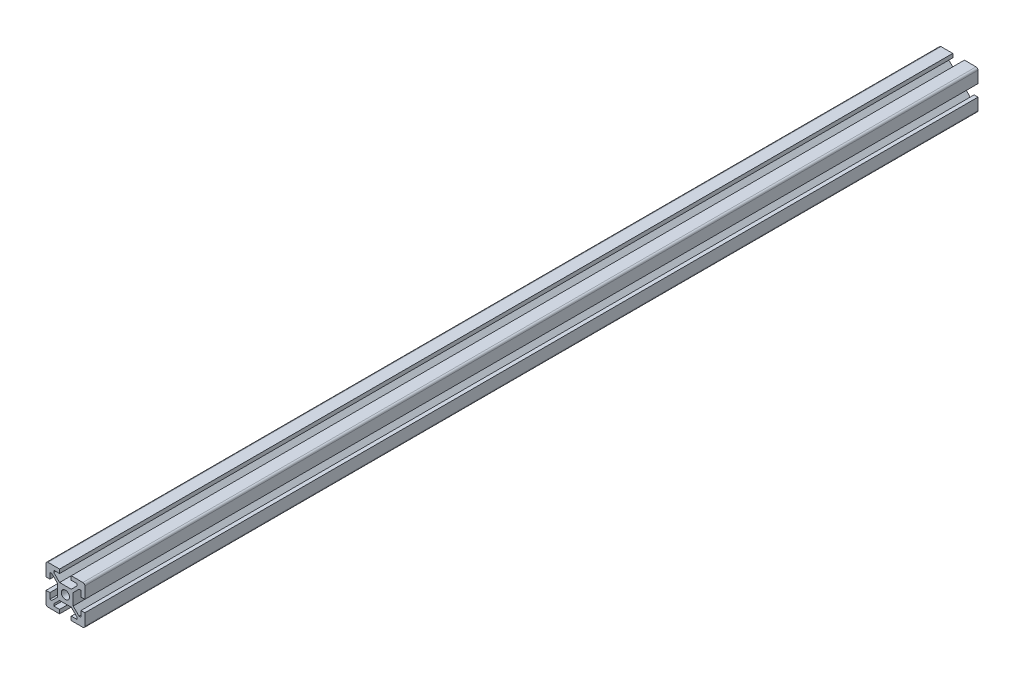
SolidWorks part; units mm, degrees
material "6063-O, Extruded Rod (SS)"
ref_plane "Piano frontale" through (0, 0, 0) normal (0, 0, 1) x (1, 0, 0)
ref_plane "Piano superiore" through (0, 0, 0) normal (0, 1, 0) x (1, 0, 0)
ref_plane "Piano destro" through (0, 0, 0) normal (1, 0, 0) x (0, 0, -1)
other "Lunghezza"
sketch "Schizzo1" plane through (0, 0, 0) normal (0, 0, 1) x (1, 0, 0)
  line L0 (-6, 8) -> (6, 8) construction
  line L1 (10, 3) -> (10, 10)
  line L2 (8, 3) -> (10, 3)
  line L3 (10, 10) -> (3, 10)
  line L4 (8, 6) -> (8, 3)
  line L5 (10, -10) -> (-10, 10) construction
  line L6 (10, 10) -> (-10, -10) construction
  line L7 (0, 23.5419) -> (0, -15.5419) construction
  line L8 (-13.4777, 0) -> (13.4408, 0) construction
  line L9 (-3, 4) -> (3, 4) construction
  line L10 (3, 4) -> (9, 10) construction
  line L11 (6, 11.4787) -> (6, 3.0667) construction
  line L12 (-6, 11.4787) -> (-6, 3.0667) construction
  line L13 (-3, 4) -> (-9, 10) construction
  line L14 (-3, 4) -> (-6, 7)
  line L15 (-6, 7) -> (-6, 8)
  line L16 (-6, 8) -> (-3, 8)
  line L17 (6, 8) -> (6, 7)
  line L18 (6, 7) -> (3, 4)
  line L19 (3, 4) -> (-3, 4)
  line L20 (-3, 8) -> (-3, 10)
  line L21 (6, 8) -> (3, 8)
  line L22 (3, 8) -> (3, 10)
  line L23 (-3, 10) -> (-10, 10)
  line L24 (7, 6) -> (8, 6)
  line L25 (4, 3) -> (7, 6)
  line L26 (4, -3) -> (4, 3)
  line L27 (7, -6) -> (4, -3)
  line L28 (8, -6) -> (7, -6)
  line L29 (8, -6) -> (8, -3)
  line L30 (8, -3) -> (10, -3)
  line L31 (10, -10) -> (10, -3)
  line L32 (3, -10) -> (10, -10)
  line L33 (3, -8) -> (3, -10)
  line L34 (6, -8) -> (3, -8)
  line L35 (6, -7) -> (6, -8)
  line L36 (3, -4) -> (6, -7)
  line L37 (-3, -4) -> (3, -4)
  line L38 (-6, -7) -> (-3, -4)
  line L39 (-6, -8) -> (-6, -7)
  line L40 (-6, -8) -> (-3, -8)
  line L41 (-3, -8) -> (-3, -10)
  line L42 (-10, -10) -> (-3, -10)
  line L43 (-10, -3) -> (-10, -10)
  line L44 (-8, -3) -> (-10, -3)
  line L45 (-8, -6) -> (-8, -3)
  line L46 (-7, -6) -> (-8, -6)
  line L47 (-4, -3) -> (-7, -6)
  line L48 (-4, 3) -> (-4, -3)
  line L49 (-7, 6) -> (-4, 3)
  line L50 (-8, 6) -> (-7, 6)
  line L51 (-8, 6) -> (-8, 3)
  line L52 (-8, 3) -> (-10, 3)
  line L53 (-10, 10) -> (-10, 3)
  circle A0 centre (0, 0) radius 2.1
  point P0 (0, 0)
  point P10 (0, 8)
  point P17 (0, 4)
  point P69 (0, 0)
  dimension "D6" = 4.2
  dimension "D1" = 20
  dimension "D2" = 10
  dimension "D3" = 2
  dimension "D4" = 12
  dimension "D5" = 4
  dimension "D7" = 4
  dimension "D8" = 6
  dimension "D9" = 6
  dimension "D10" = 3
  dimension "D11" = 4
extrude "Estrusione-Estrusione1" add sketch "Schizzo1" along normal blind 460
fillet "Raccordo1" radius 1 4 edges at (-10, -10, 230) (10, -10, 230) (-10, 10, 230) (10, 10, 230)
sketch "Sketch1" [suppressed] plane through (0, 0, 0) normal (1, 0, 0) x (0, 0, -1)
  line L0 (-150, 10) -> (-150, -10) construction
  line L1 (-300, 10) -> (0, 10) construction
  line L2 (0, -10) -> (-300, -10) construction
